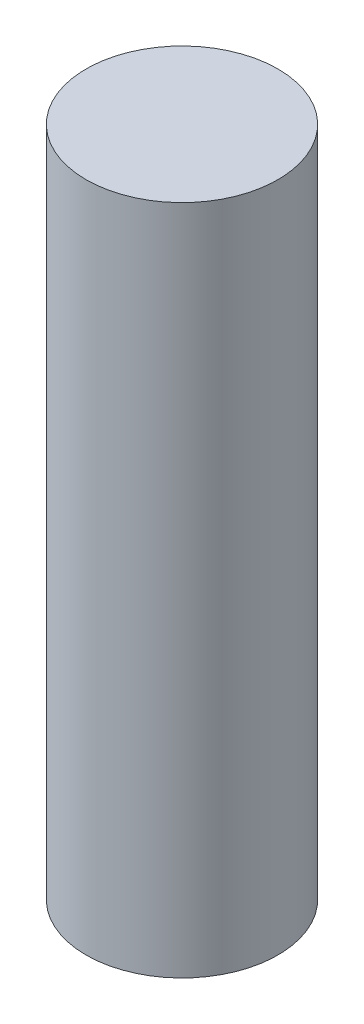
SolidWorks part; units mm, degrees
ref_plane "Front Plane" through (0, 0, 0) normal (0, 0, 1) x (1, 0, 0)
ref_plane "Top Plane" through (0, 0, 0) normal (0, 1, 0) x (1, 0, 0)
ref_plane "Right Plane" through (0, 0, 0) normal (1, 0, 0) x (0, 0, -1)
sketch "Sketch1" plane through (0, 0, 0) normal (0, 1, 0) x (1, 0, 0)
  circle A0 centre (0, 0) radius 5
  dimension "D1" = 10
extrude "Boss-Extrude1" add sketch "Sketch1" along normal mid plane 35
